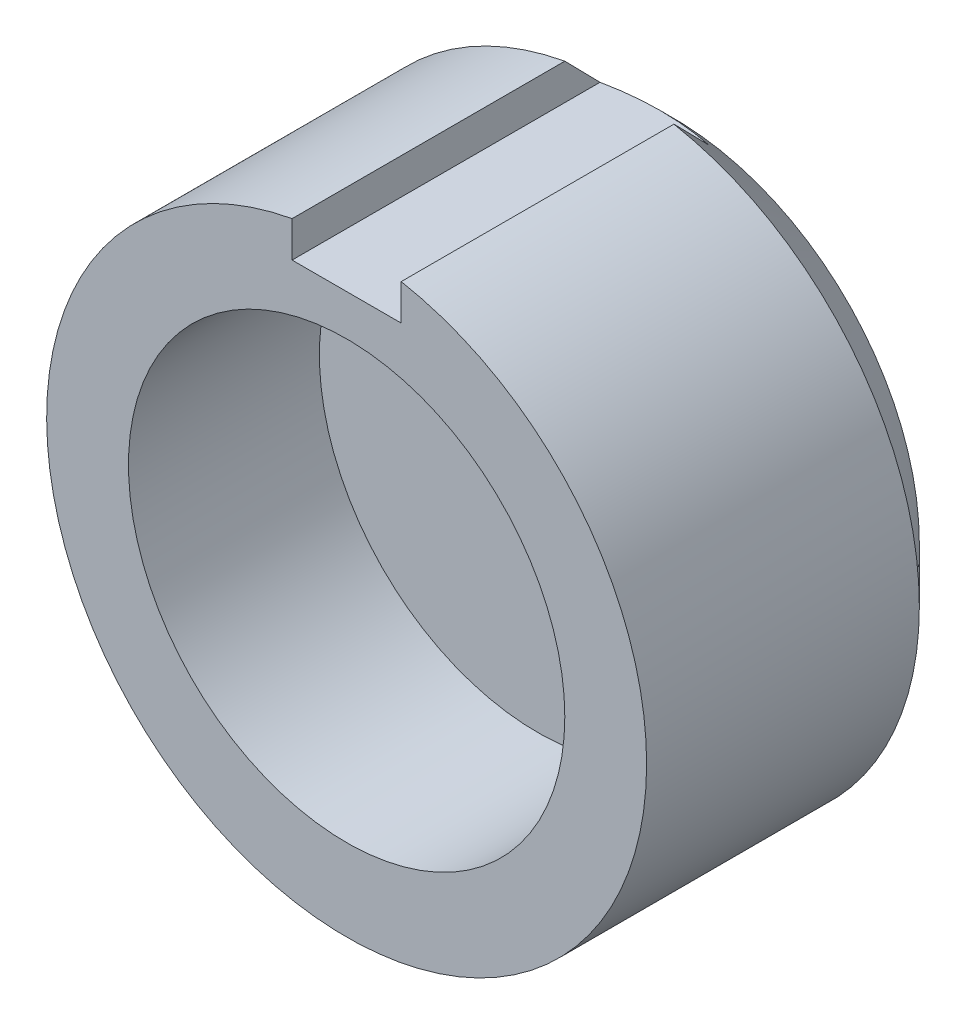
SolidWorks part; units mm, degrees
material "201 Annealed Stainless Steel (SS)"
ref_plane "Front" through (0, 0, 0) normal (0, 0, 1) x (1, 0, 0)
ref_plane "Top" through (0, 0, 0) normal (0, 1, 0) x (1, 0, 0)
ref_plane "Right" through (0, 0, 0) normal (1, 0, 0) x (0, 0, -1)
sketch "Sketch1" plane through (0, 0, 0) normal (0, 0, 1) x (1, 0, 0)
  circle A0 centre (0, 0) radius 11
  dimension "D1" = 22
extrude "Boss-Extrude1" add sketch "Sketch1" along normal blind 12
sketch "Sketch2" plane through (0, 0, 12) normal (0, 0, 1) x (1, 0, 0)
  circle A0 centre (0, 0) radius 8
  dimension "D1" = 16
extrude "Cut-Extrude1" cut sketch "Sketch2" against normal blind 7
chamfer "Chamfer1" distance 2 angle 45 1 edges at (11, 0, 0)
sketch "Sketch3" plane through (0, 0, 12) normal (0, 0, 1) x (1, 0, 0)
  line L1 (2, 12.7889) -> (-2, 12.7889)
  line L2 (2, 12.7889) -> (2, 9.5)
  line L3 (2, 9.5) -> (-2, 9.5)
  line L4 (-2, 12.7889) -> (-2, 9.5)
  circle A0 centre (0, 0) radius 11 construction
  point P4 (0, 9.5)
  dimension "D2" = 1.5
  dimension "D1" = 4
  dimension "D3" = 3.2889
extrude "Cut-Extrude2" cut sketch "Sketch3" against normal blind 22
